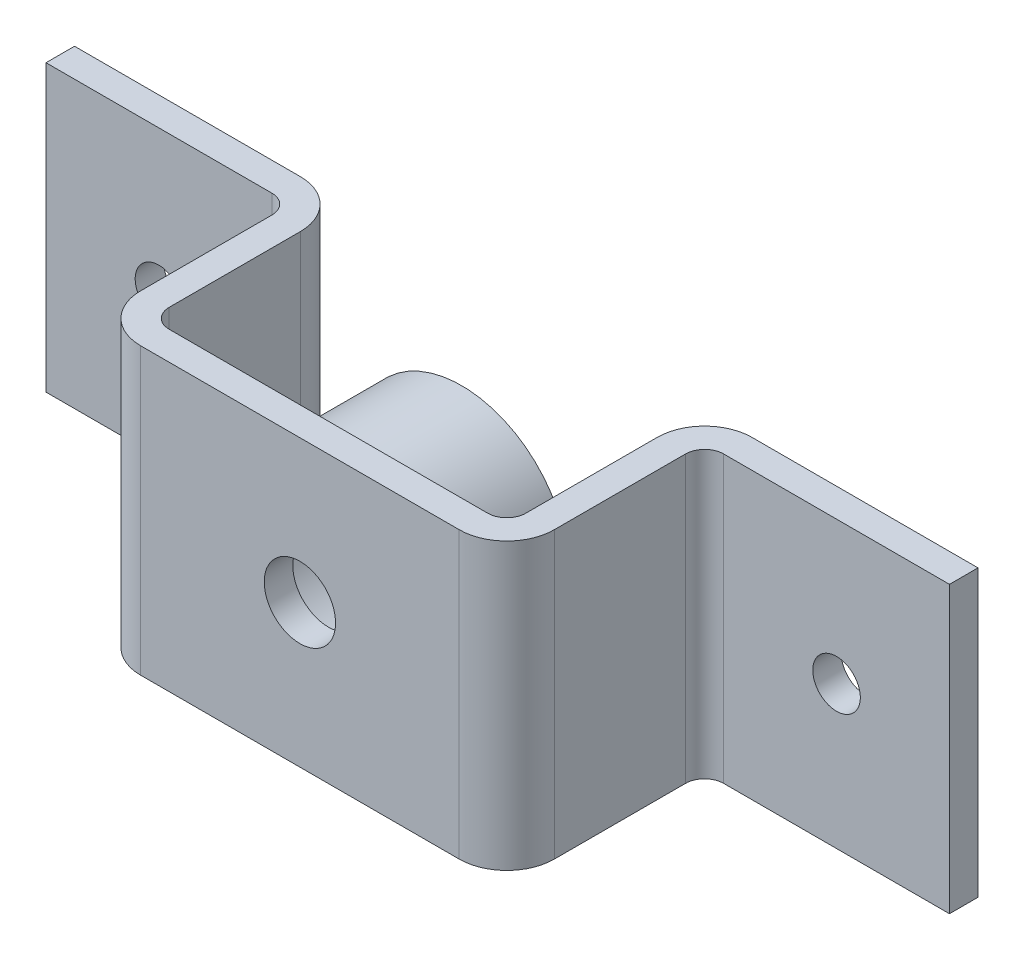
SolidWorks part; units mm, degrees
ref_plane "Front Plane" through (0, 0, 0) normal (0, 0, 1) x (1, 0, 0)
ref_plane "Top Plane" through (0, 0, 0) normal (0, 1, 0) x (1, 0, 0)
ref_plane "Right Plane" through (0, 0, 0) normal (1, 0, 0) x (0, 0, -1)
sketch "Sketch1" plane through (0, 0, 0) normal (0, 0, 1) x (1, 0, 0)
  line L1 (-475, -150) -> (475, -150)
  line L2 (-475, -150) -> (-475, 150)
  line L3 (-475, 150) -> (475, 150)
  line L4 (475, -150) -> (475, 150)
  point P0 (0, 0)
  dimension "D1" = 300
  dimension "D2" = 950
extrude "Boss-Extrude1" add sketch "Sketch1" against normal blind 238
sketch "Sketch2" plane through (0, 150, 0) normal (0, 1, 0) x (1, 0, 0)
  line L0 (-187.5, 238) -> (187.5, 238)
  line L1 (475, 238) -> (-475, 238) construction
  line L4 (187.5, 30) -> (-187.5, 30)
  line L5 (-187.5, 238) -> (-187.5, 30)
  line L6 (187.5, 238) -> (187.5, 30)
  point P5 (0, 238)
extrude "Cut-Extrude1" cut sketch "Sketch2" against normal blind 305
sketch "Sketch3" plane through (0, -150, 0) normal (0, -1, 0) x (1, 0, 0)
  line L0 (187.5, -30) -> (187.5, -238) construction
  line L1 (475, 0) -> (217.5, 0)
  line L2 (475, 0) -> (475, -208)
  line L3 (475, -208) -> (217.5, -208)
  line L4 (217.5, 0) -> (217.5, -208)
  line L5 (475, -238) -> (187.5, -238) construction
  line L8 (-475, 0) -> (-217.5, 0)
  line L9 (-475, 0) -> (-475, -208)
  line L10 (-475, -208) -> (-217.5, -208)
  line L11 (-217.5, 0) -> (-217.5, -208)
  dimension "D1" = 30
  dimension "D2" = 30
extrude "Cut-Extrude2" cut sketch "Sketch3" against normal blind 305
fillet "Fillet2" radius 20 4 edges at (217.5, 0, -208) (-217.5, 0, -208) (187.5, 0, -30) (-187.5, 0, -30)
fillet "Fillet3" radius 50 4 edges at (-217.5, 0, 0) (217.5, 0, 0) (187.5, 0, -238) (-187.5, 0, -238)
sketch "Sketch4" plane through (0, 0, -30) normal (0, 0, -1) x (-1, 0, 0)
  circle A0 centre (0, 0) radius 112.5
  circle A1 centre (0, 0) radius 87.5
  dimension "D1" = 112.5
  dimension "D2" = 87.5
extrude "Boss-Extrude2" add sketch "Sketch4" along normal blind 140
sketch "Sketch5" plane through (0, 0, -30) normal (0, 0, -1) x (-1, 0, 0)
  circle A0 centre (0, 0) radius 37.5
  dimension "D1" = 37.5
extrude "Cut-Extrude3" cut sketch "Sketch5" against normal blind 75
sketch "Sketch6" plane through (0, 0, -238) normal (0, 0, -1) x (-1, 0, 0)
  circle A0 centre (-356.25, 0) radius 25
  dimension "D1" = 25
extrude "Cut-Extrude4" cut sketch "Sketch6" against normal blind 39
mirror "Mirror1" about plane through (0, 0, 0) normal (1, 0, 0) of "Cut-Extrude4"
